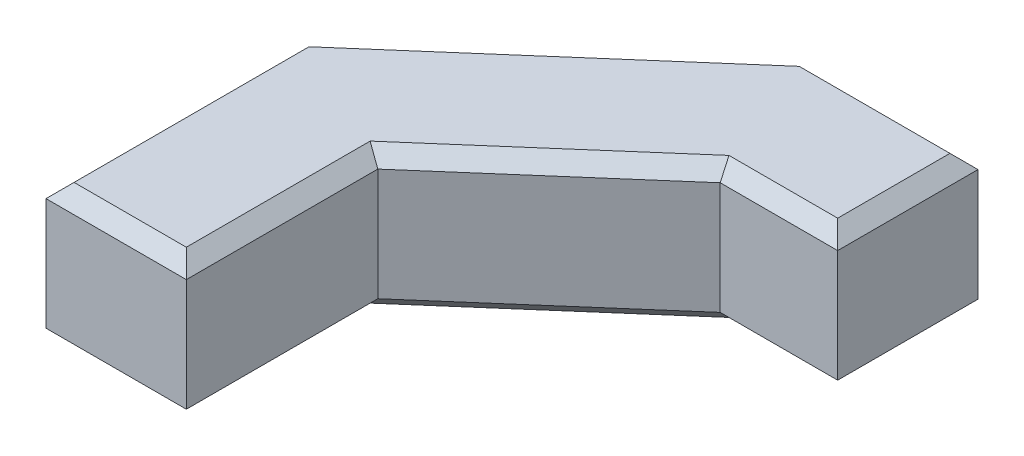
SolidWorks part; units mm, degrees
ref_plane "Front Plane" through (0, 0, 0) normal (0, 0, 1) x (1, 0, 0)
ref_plane "Top Plane" through (0, 0, 0) normal (0, 1, 0) x (1, 0, 0)
ref_plane "Right Plane" through (0, 0, 0) normal (1, 0, 0) x (0, 0, -1)
sketch "Sketch1" plane through (0, 0, 0) normal (0, 1, 0) x (1, 0, 0)
  line L0 (42.8304, 91.3481) -> (18.6017, 91.3481)
  line L1 (18.6017, 91.3481) -> (-20, 57.7418)
  line L2 (-20, 57.7418) -> (-20, 21.3481)
  line L3 (-20, 21.3481) -> (0, 21.3481)
  line L4 (0, 21.3481) -> (0, 48.6363)
  line L5 (0, 48.6363) -> (26.0878, 71.3481)
  line L6 (26.0878, 71.3481) -> (42.8304, 71.3481)
  line L7 (42.8304, 71.3481) -> (42.8304, 91.3481)
  point P2 (-3.8806, 59.058)
  point P10 (9.0148, 46.6461)
  point P11 (0, 27.6253)
  point P12 (-1.6239, 65.5057)
  point P13 (0, 0)
  point P14 (50.2576, 63.8266)
  point P15 (5.5581, 60.7197)
  point P16 (10.5735, 73.1017)
  point P17 (-20, 49.1214)
  point P18 (23.269, 90.3424)
  point P19 (-20, 57.7418)
  point P20 (0, 13.2294)
  point P21 (41.4501, 85.0135)
  point P22 (0, 16.3641)
  point P23 (44.0802, 83.0496)
  point P24 (42.8304, 65.4277)
  point P25 (17.5848, 84.0494)
  point P26 (23.4588, 66.9274)
  point P27 (26.0878, 71.3481)
  dimension "D1" = 20
  dimension "D2" = 20
  dimension "D3" = 20
  dimension "D4" = 70
  dimension "D5" = 51.1808
  dimension "D6" = 34.5891
  dimension "D7" = 24.2288
extrude "Boss-Extrude1" add sketch "Sketch1" along normal blind 20
chamfer "Chamfer1" distance 2 angle 45 16 edges at (30.7161, 0, -91.3481) (-0.6992, 0, -74.545) (-20, 0, -39.545) (-10, 0, -21.3481) (0, 0, -34.9922) (13.0439, 0, -59.9922) (34.4591, 0, -71.3481) (42.8304, 0, -81.3481) (34.4591, 20, -71.3481) (13.0439, 20, -59.9922) (0, 20, -34.9922) (-10, 20, -21.3481) (-20, 20, -39.545) (-0.6992, 20, -74.545) (30.7161, 20, -91.3481) (42.8304, 20, -81.3481)
